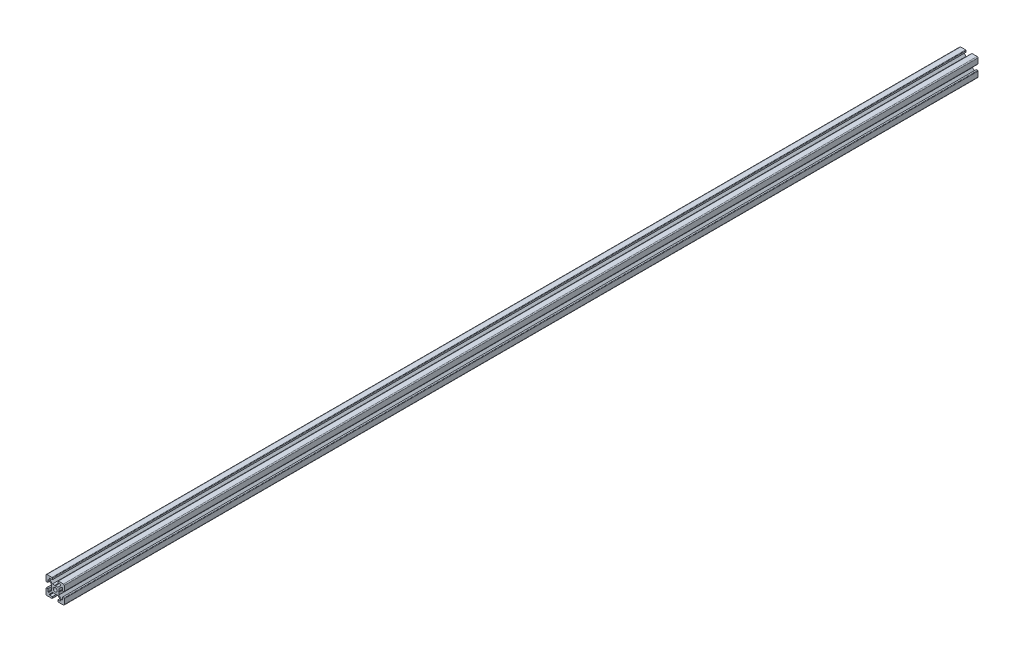
SolidWorks part; units mm, degrees
material "Lega 6061"
ref_plane "Piano frontale" through (0, 0, 0) normal (0, 0, 1) x (1, 0, 0)
ref_plane "Piano superiore" through (0, 0, 0) normal (0, 1, 0) x (1, 0, 0)
ref_plane "Piano destro" through (0, 0, 0) normal (1, 0, 0) x (0, 0, -1)
sketch "Schizzo1" plane through (0, 0, 0) normal (0, 0, 1) x (1, 0, 0)
  line L0 (0, 0) -> (-10, 0) construction
  line L1 (0, 0) -> (0, 10) construction
  line L2 (-3.6, 0) -> (-4, 0.4)
  line L3 (-4, 0.4) -> (-4, 3)
  line L4 (-4, 3) -> (-7, 6)
  line L5 (-7, 6) -> (-8, 6)
  line L6 (-8, 6) -> (-8, 3)
  line L7 (-8, 3) -> (-9.5, 3)
  line L8 (-10, 3.5) -> (-10, 9)
  line L9 (0, 0) -> (-10, 10) construction
  line L10 (0, 3.6) -> (-0.4, 4)
  line L11 (-0.4, 4) -> (-3, 4)
  line L12 (-3, 4) -> (-6, 7)
  line L13 (-6, 7) -> (-6, 8)
  line L14 (-6, 8) -> (-3, 8)
  line L15 (-3, 8) -> (-3, 9.5)
  line L16 (-3.5, 10) -> (-9, 10)
  line L17 (0, 0) -> (-10, -10) construction
  line L18 (-3.5, -10) -> (-9, -10)
  line L19 (-3, -8) -> (-3, -9.5)
  line L20 (-6, -8) -> (-3, -8)
  line L21 (-6, -7) -> (-6, -8)
  line L22 (-3, -4) -> (-6, -7)
  line L23 (-0.4, -4) -> (-3, -4)
  line L24 (0, -3.6) -> (-0.4, -4)
  line L25 (-10, -3.5) -> (-10, -9)
  line L26 (-8, -3) -> (-9.5, -3)
  line L27 (-8, -6) -> (-8, -3)
  line L28 (-7, -6) -> (-8, -6)
  line L29 (-4, -3) -> (-7, -6)
  line L30 (-4, -0.4) -> (-4, -3)
  line L31 (-3.6, 0) -> (-4, -0.4)
  line L32 (0, 0) -> (10, -10) construction
  line L33 (0, 0) -> (10, 10) construction
  line L34 (3.6, 0) -> (4, -0.4)
  line L35 (4, -0.4) -> (4, -3)
  line L36 (4, -3) -> (7, -6)
  line L37 (7, -6) -> (8, -6)
  line L38 (8, -6) -> (8, -3)
  line L39 (8, -3) -> (9.5, -3)
  line L40 (10, -3.5) -> (10, -9)
  line L41 (0, -3.6) -> (0.4, -4)
  line L42 (0.4, -4) -> (3, -4)
  line L43 (3, -4) -> (6, -7)
  line L44 (6, -7) -> (6, -8)
  line L45 (6, -8) -> (3, -8)
  line L46 (3, -8) -> (3, -9.5)
  line L47 (3.5, -10) -> (9, -10)
  line L48 (3.5, 10) -> (9, 10)
  line L49 (3, 8) -> (3, 9.5)
  line L50 (6, 8) -> (3, 8)
  line L51 (6, 7) -> (6, 8)
  line L52 (3, 4) -> (6, 7)
  line L53 (0.4, 4) -> (3, 4)
  line L54 (0, 3.6) -> (0.4, 4)
  line L55 (10, 3.5) -> (10, 9)
  line L56 (8, 3) -> (9.5, 3)
  line L57 (8, 6) -> (8, 3)
  line L58 (7, 6) -> (8, 6)
  line L59 (4, 3) -> (7, 6)
  line L60 (4, 0.4) -> (4, 3)
  line L61 (3.6, 0) -> (4, 0.4)
  arc A0 (-10, 9) -> (-9, 10) centre (-9, 9) cw
  arc A1 (-3, 9.5) -> (-3.5, 10) centre (-3.5, 9.5) ccw
  arc A2 (-9.5, 3) -> (-10, 3.5) centre (-9.5, 3.5) cw
  arc A3 (-9.5, -3) -> (-10, -3.5) centre (-9.5, -3.5) ccw
  arc A4 (-3, -9.5) -> (-3.5, -10) centre (-3.5, -9.5) cw
  arc A5 (-10, -9) -> (-9, -10) centre (-9, -9) ccw
  arc A6 (10, -9) -> (9, -10) centre (9, -9) cw
  arc A7 (3, -9.5) -> (3.5, -10) centre (3.5, -9.5) ccw
  arc A8 (9.5, -3) -> (10, -3.5) centre (9.5, -3.5) cw
  arc A9 (9.5, 3) -> (10, 3.5) centre (9.5, 3.5) ccw
  arc A10 (3, 9.5) -> (3.5, 10) centre (3.5, 9.5) cw
  arc A11 (10, 9) -> (9, 10) centre (9, 9) ccw
  circle A12 centre (0, 0) radius 2.1
  point P24 (-3, 10)
  point P27 (-10, 3)
  point P49 (-10, -3)
  point P50 (-3, -10)
  point P92 (3, -10)
  point P93 (10, -3)
  point P94 (10, 3)
  point P95 (3, 10)
  dimension "D2" = 1
  dimension "D12" = 0.5
  dimension "D13" = 4.2
  dimension "D3" = 8
  dimension "D4" = 0.4
  dimension "D5" = 45
  dimension "D6" = 6
  dimension "D7" = 12
  dimension "D8" = 20
  dimension "D9" = 2
  dimension "D10" = 4
  dimension "D11" = 45
extrude "Estrusione-Estrusione1" add sketch "Schizzo1" along normal blind 1000
